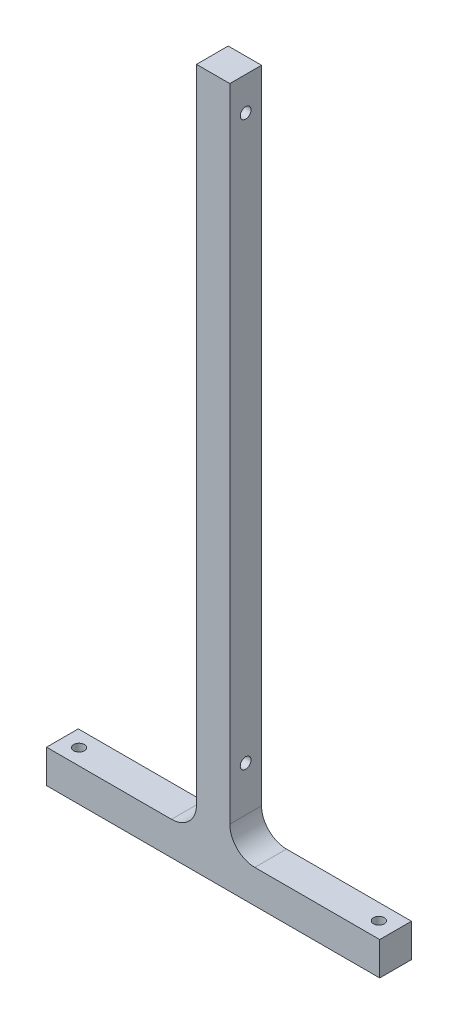
SolidWorks part; units mm, degrees
ref_plane "Front Plane" through (0, 0, 0) normal (0, 0, 1) x (1, 0, 0)
ref_plane "Top Plane" through (0, 0, 0) normal (0, 1, 0) x (1, 0, 0)
ref_plane "Right Plane" through (0, 0, 0) normal (1, 0, 0) x (0, 0, -1)
sketch "Sketch1" plane through (0, 0, 0) normal (0, 0, 1) x (1, 0, 0)
  line L0 (0, 0) -> (0, 210) construction
  line L1 (-50, 0) -> (50, 0)
  line L2 (50, 0) -> (50, 10)
  line L3 (50, 10) -> (5, 10)
  line L4 (5, 10) -> (5, 210)
  line L5 (5, 210) -> (-5, 210)
  line L6 (-5, 210) -> (-5, 10)
  line L7 (-5, 10) -> (-50, 10)
  line L8 (-50, 10) -> (-50, 0)
  dimension "D1" = 10
  dimension "D2" = 100
  dimension "D3" = 210
extrude "Boss-Extrude1" add sketch "Sketch1" along normal blind 9.525
fillet "Fillet1" radius 7.5 2 edges at (-5, 10, 4.7625) (5, 10, 4.7625)
sketch "Sketch2" plane through (0, 10, 0) normal (0, 1, 0) x (1, 0, 0)
  line L0 (-50, -4.7625) -> (-45, -4.7625) construction
  line L1 (-50, -9.525) -> (-50, 0) construction
  line L2 (0, 0) -> (0, -9.525) construction
  line L3 (5, -9.525) -> (-5, -9.525) construction
  circle A0 centre (-45, -4.7625) radius 1.625
  circle A1 centre (45, -4.7625) radius 1.625
  dimension "D1" = 3.25
  dimension "D2" = 5
extrude "Cut-Extrude1" cut sketch "Sketch2" against normal through all
sketch "Sketch3" plane through (-5, 0, 0) normal (-1, 0, 0) x (0, 0, 1)
  line L0 (4.7625, 210) -> (4.7625, 0) construction
  line L1 (9.525, 210) -> (0, 210) construction
  line L2 (9.525, 0) -> (0, 0) construction
  circle A0 centre (4.7625, 31) radius 1.625
  circle A1 centre (4.7625, 200) radius 1.625
  dimension "D1" = 3.25
  dimension "D2" = 31
  dimension "D3" = 200
extrude "Cut-Extrude2" cut sketch "Sketch3" against normal through all
